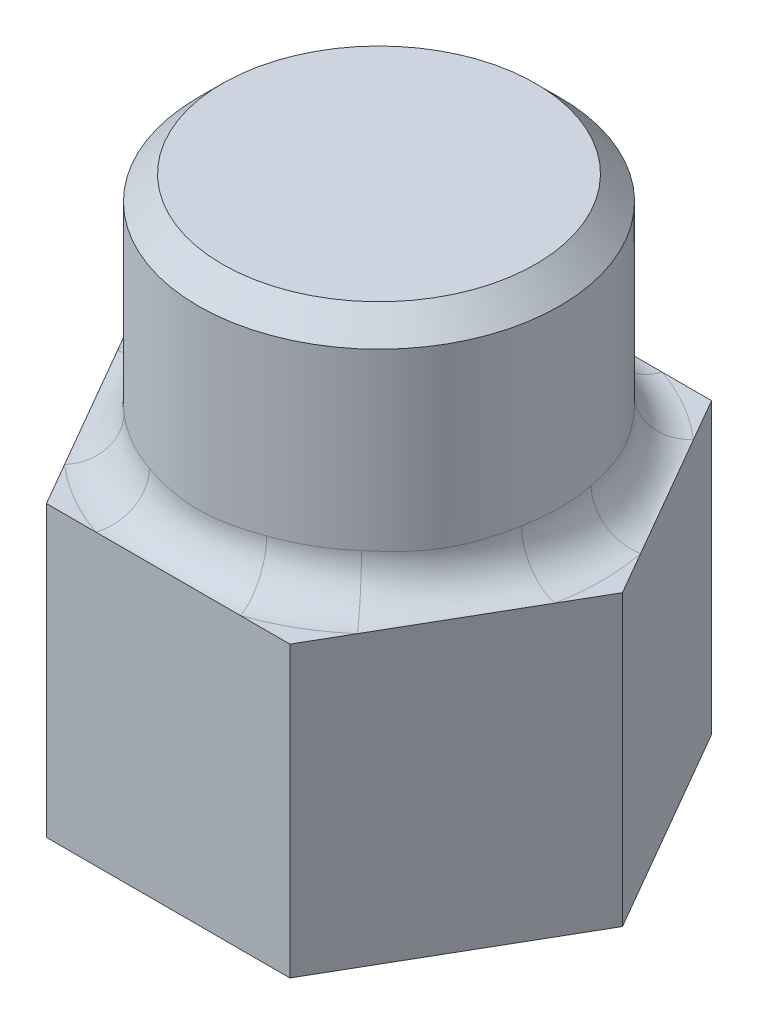
SolidWorks part; units mm, degrees
ref_plane "Спереди" through (0, 0, 0) normal (0, 0, 1) x (1, 0, 0)
ref_plane "Сверху" through (0, 0, 0) normal (0, 1, 0) x (1, 0, 0)
ref_plane "Справа" through (0, 0, 0) normal (1, 0, 0) x (0, 0, -1)
sketch "Эскиз1" plane through (0, 0, 0) normal (0, 1, 0) x (1, 0, 0)
  line L1 (4.0415, 0) -> (2.0207, 3.5)
  line L2 (2.0207, 3.5) -> (-2.0207, 3.5)
  line L3 (-2.0207, 3.5) -> (-4.0415, 0)
  line L4 (-4.0415, 0) -> (-2.0207, -3.5)
  line L5 (-2.0207, -3.5) -> (2.0207, -3.5)
  line L6 (2.0207, -3.5) -> (4.0415, 0)
  circle A0 centre (0, 0) radius 3.5 construction
  dimension "D1" = 7
extrude "Бобышка-Вытянуть1" add sketch "Эскиз1" along normal blind 4.8 contours L2 L3 L4 L5 L6 L1
sketch "Эскиз2" plane through (0, 4.8, 0) normal (0, 1, 0) x (1, 0, 0)
  circle A0 centre (0, 0) radius 3
  dimension "D1" = 6
extrude "Бобышка-Вытянуть2" add sketch "Эскиз2" along normal blind 4 contours A0
fillet "Скругление4" radius 0.7 1 edges at (0, 4.8, 3)
chamfer "Фаска1" distance 0.4 angle 45 1 edges at (0, 8.8, 3)
